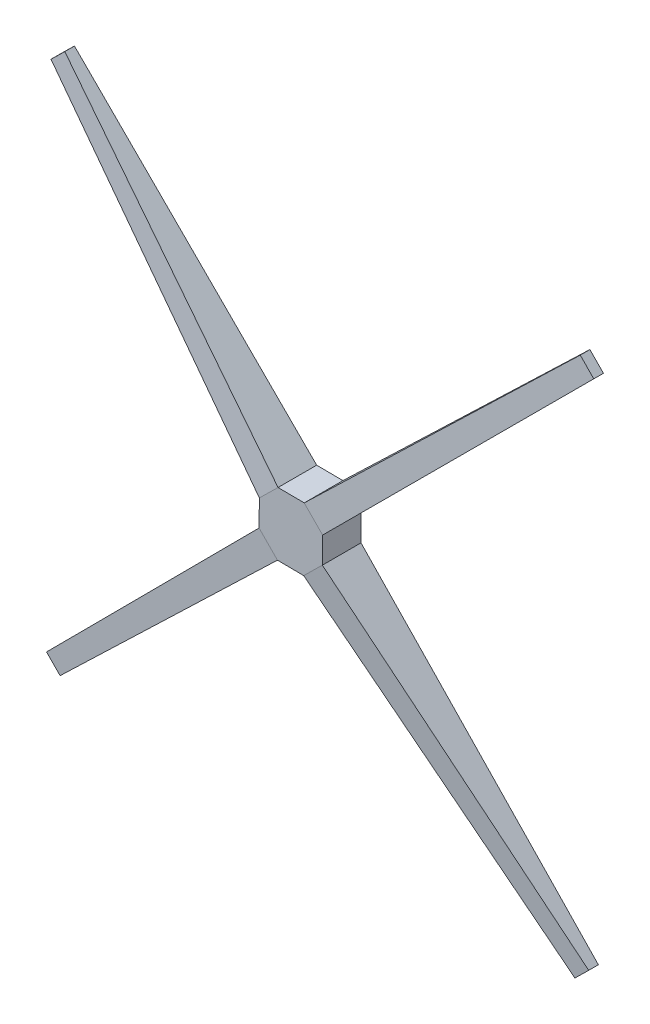
SolidWorks part; units mm, degrees
ref_plane "Front Plane" through (0, 0, 0) normal (0, 0, 1) x (1, 0, 0)
ref_plane "Top Plane" through (0, 0, 0) normal (0, 1, 0) x (1, 0, 0)
ref_plane "Right Plane" through (0, 0, 0) normal (1, 0, 0) x (0, 0, -1)
ref_plane "Plane1" through (0, 0, -20) normal (0, 0, -1) x (-1, 0, 0)
sketch "Sketch2" plane through (0, 0, -20) normal (0, 0, -1) x (-1, 0, 0)
  circle A0 centre (600.7379, 0) radius 45
ref_plane "Plane2" through (0, 0, 0) normal (0, 0, 1) x (1, 0, 0)
sketch "Sketch3" plane through (0, 0, 0) normal (0, 0, 1) x (1, 0, 0)
  line L1 (-583.1332, 41.4135) -> (-617.5733, 41.7321)
  line L2 (-617.5733, 41.7321) -> (-642.1513, 17.6046)
  line L3 (-642.1513, 17.6046) -> (-642.47, -16.8354)
  line L4 (-642.47, -16.8354) -> (-618.3425, -41.4135)
  line L5 (-618.3425, -41.4135) -> (-583.9025, -41.7321)
  line L6 (-583.9025, -41.7321) -> (-559.3244, -17.6046)
  line L7 (-559.3244, -17.6046) -> (-559.0057, 16.8354)
  line L8 (-559.0057, 16.8354) -> (-583.1332, 41.4135)
  circle A0 centre (-600.7379, 0) radius 41.5746 construction
extrude "Boss-Extrude1" add sketch "Sketch3" along normal blind 50.8
ref_plane "Plane3" through (-335.5948, -329.4419, 0) normal (-0.7136, -0.7005, 0) x (0, 0, 1)
ref_plane "Plane4" through (-656.723, -644.6826, 0) normal (-0.7136, -0.7005, 0) x (0, 0, 1)
sketch "Sketch5" plane through (-335.5948, -329.4419, 0) normal (-0.7136, -0.7005, 0) x (0, 0, 1)
  line L1 (50.8, 438.0585) -> (0, 438.0585)
  line L2 (50.8, 438.0585) -> (50.8, 403.617)
  line L3 (50.8, 403.617) -> (0, 403.617)
  line L4 (0, 438.0585) -> (0, 403.617)
sketch "Sketch8" plane through (-656.723, -644.6826, 0) normal (-0.7136, -0.7005, 0) x (0, 0, 1)
  line L0 (0, 407.5013) -> (12.7, 407.5013)
  line L1 (0, 407.5013) -> (0, 432.9013)
  line L2 (12.7, 407.5013) -> (12.7, 432.9013)
  line L3 (0, 432.9013) -> (12.7, 432.9013)
  line L4 (0, 407.5013) -> (12.7, 432.9013) construction
  line L5 (12.7, 407.5013) -> (0, 432.9013) construction
  line L6 (0, 438.0585) -> (0, 403.617) construction
  point P0 (12.2617, 420.8377)
  point P1 (6.35, 420.2013)
loft "Loft1" add profiles "Sketch5", "Sketch8"
ref_plane "Plane5" through (44.8702, 44.0475, 0) normal (0.7136, 0.7005, 0) x (0, 0, -1)
sketch "Sketch10" plane through (44.8702, 44.0475, 0) normal (0.7136, 0.7005, 0) x (0, 0, -1)
  line L1 (-12.7, 432.9013) -> (0, 432.9013)
  line L2 (-12.7, 432.9013) -> (-12.7, 407.5013)
  line L3 (-12.7, 407.5013) -> (0, 407.5013)
  line L4 (0, 432.9013) -> (0, 407.5013)
ref_plane "Plane6" through (-276.258, -271.1931, 0) normal (0.7136, 0.7005, 0) x (0, 0, -1)
sketch "Sketch11" plane through (-276.258, -271.1931, 0) normal (0.7136, 0.7005, 0) x (0, 0, -1)
  line L1 (-50.8, 438.0585) -> (0, 438.0585)
  line L2 (-50.8, 438.0585) -> (-50.8, 403.617)
  line L3 (-50.8, 403.617) -> (0, 403.617)
  line L4 (0, 438.0585) -> (0, 403.617)
loft "Loft2" add profiles "Sketch11", "Sketch10"
ref_plane "Plane7" through (-265.687, 270.6491, 0) normal (0.7005, -0.7136, 0) x (-0.7136, -0.7005, 0)
ref_plane "Plane8" through (49.5536, -50.4791, 0) normal (0.7005, -0.7136, 0) x (-0.7136, -0.7005, 0)
sketch "Sketch12" plane through (-265.687, 270.6491, 0) normal (0.7005, -0.7136, 0) x (-0.7136, -0.7005, 0)
  line L1 (411.4768, 0) -> (445.9183, 0)
  line L2 (411.4768, 0) -> (411.4768, -50.8)
  line L3 (411.4768, -50.8) -> (445.9183, -50.8)
  line L4 (445.9183, 0) -> (445.9183, -50.8)
sketch "Sketch13" plane through (49.5536, -50.4791, 0) normal (0.7005, -0.7136, 0) x (-0.7136, -0.7005, 0)
  line L0 (411.4768, 0) -> (445.9183, 0) construction
  line L1 (415.9568, 0) -> (441.3568, 0)
  line L2 (415.9568, 0) -> (415.9568, -12.7)
  line L3 (415.9568, -12.7) -> (441.3568, -12.7)
  line L4 (441.3568, 0) -> (441.3568, -12.7)
  point P6 (415.9568, 0)
loft "Loft3" add profiles "Sketch12", "Sketch13"
ref_plane "Plane9" through (-323.9359, 329.9859, 0) normal (-0.7005, 0.7136, 0) x (0.7136, 0.7005, 0)
ref_plane "Plane10" through (-639.1765, 651.1141, 0) normal (-0.7005, 0.7136, 0) x (0.7136, 0.7005, 0)
sketch "Sketch14" plane through (-323.9359, 329.9859, 0) normal (-0.7005, 0.7136, 0) x (0.7136, 0.7005, 0)
  line L1 (-445.9183, 0) -> (-411.4768, 0)
  line L2 (-445.9183, 0) -> (-445.9183, -50.8)
  line L3 (-445.9183, -50.8) -> (-411.4768, -50.8)
  line L4 (-411.4768, 0) -> (-411.4768, -50.8)
sketch "Sketch15" plane through (-639.1765, 651.1141, 0) normal (-0.7005, 0.7136, 0) x (0.7136, 0.7005, 0)
  line L1 (-441.3568, 0) -> (-415.9568, 0)
  line L2 (-441.3568, 0) -> (-441.3568, -12.7)
  line L3 (-441.3568, -12.7) -> (-415.9568, -12.7)
  line L4 (-415.9568, 0) -> (-415.9568, -12.7)
loft "Loft4" add profiles "Sketch14", "Sketch15"
